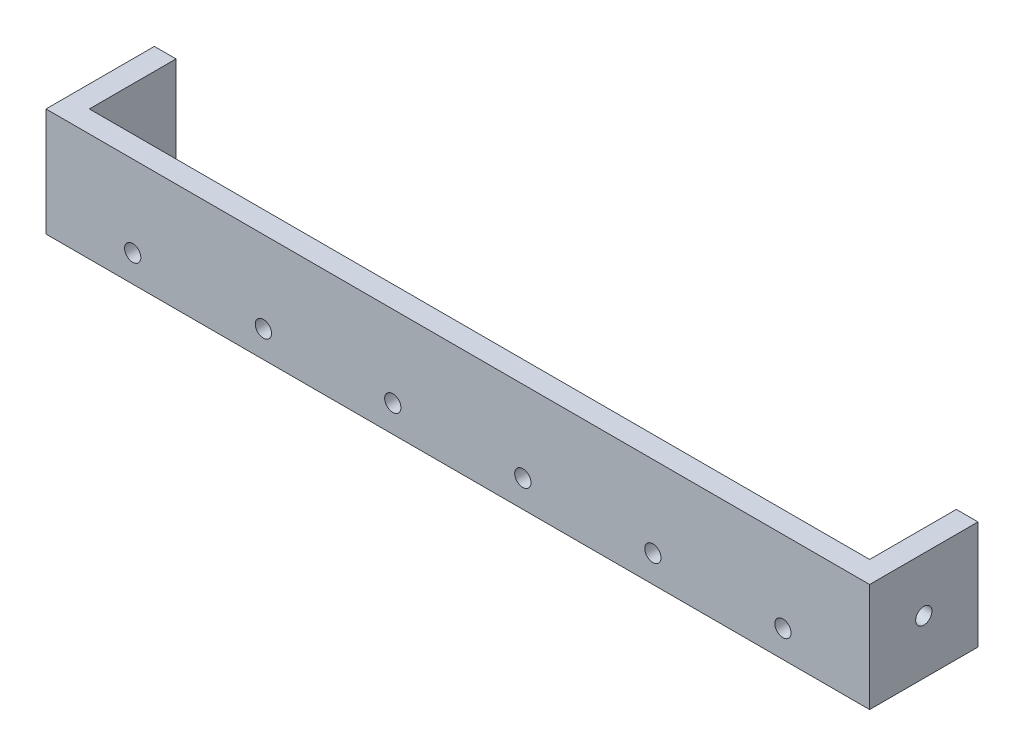
SolidWorks part; units mm, degrees
ref_plane "Front Plane" through (0, 0, 0) normal (0, 0, 1) x (1, 0, 0)
ref_plane "Top Plane" through (0, 0, 0) normal (0, 1, 0) x (1, 0, 0)
ref_plane "Right Plane" through (0, 0, 0) normal (1, 0, 0) x (0, 0, -1)
sketch "Sketch1" plane through (0, 0, 0) normal (0, 0, 1) x (1, 0, 0)
  line L0 (0, 0) -> (36, 0) construction
  line L1 (0, 0) -> (72, 0)
  line L2 (0, 0) -> (0, 10)
  line L3 (0, 10) -> (72, 10)
  line L4 (72, 0) -> (72, 10)
  line L5 (36, 0) -> (36, 18.4023) construction
sketch "Sketch3" plane through (0, 0, 0) normal (0, 0, 1) x (1, 0, 0)
  line L0 (36, 0) -> (36, 2.5) construction
  line L1 (36, 0) -> (36, 18.4023) construction
  line L2 (36, 2.5) -> (30, 2.5) construction
  line L3 (30, 2.5) -> (18, 2.5) construction
  line L4 (18, 2.5) -> (6, 2.5) construction
  line L5 (36, 2.5) -> (42, 2.5) construction
  line L6 (42, 2.5) -> (54, 2.5) construction
  line L7 (54, 2.5) -> (66, 2.5) construction
  circle A0 centre (42, 2.5) radius 0.75
  circle A1 centre (54, 2.5) radius 0.75
  circle A2 centre (66, 2.5) radius 0.75
  circle A6 centre (30, 2.5) radius 0.75
  circle A7 centre (18.0602, 2.4636) radius 0.75
  circle A8 centre (6, 2.5) radius 0.75
extrude "Boss-Extrude1" add sketch "Sketch1" along normal blind 2
extrude "Cut-Extrude2" cut sketch "Sketch3" along normal blind 2
ref_plane "Plane1" through (72, 0, 0) normal (1, 0, 0) x (0, 0, -1)
sketch "Sketch4" plane through (72, 0, 0) normal (1, 0, 0) x (0, 0, -1)
  line L1 (-2, 10) -> (8, 10)
  line L2 (-2, 10) -> (-2, 0)
  line L3 (-2, 0) -> (8, 0)
  line L4 (8, 10) -> (8, 0)
extrude "Boss-Extrude2" add sketch "Sketch4" along normal blind 2
sketch "Sketch5" plane through (72, 0, 0) normal (1, 0, 0) x (0, 0, -1)
  line L0 (-2, 10) -> (-2, 5) construction
  line L1 (-2, 10) -> (-2, 0) construction
  line L2 (-2, 5) -> (3, 5) construction
  circle A0 centre (3, 5) radius 0.75
extrude "Cut-Extrude4" cut sketch "Sketch5" along normal blind 2
ref_plane "Plane2" through (0, 0, 0) normal (-1, 0, 0) x (0, 0, 1)
sketch "Sketch6" plane through (0, 0, 0) normal (-1, 0, 0) x (0, 0, 1)
  line L1 (2, 0) -> (-8, 0)
  line L2 (2, 0) -> (2, 10)
  line L3 (2, 10) -> (-8, 10)
  line L4 (-8, 0) -> (-8, 10)
extrude "Boss-Extrude3" add sketch "Sketch6" along normal blind 2
sketch "Sketch7" plane through (0, 0, 0) normal (-1, 0, 0) x (0, 0, 1)
  line L3 (-3, 0) -> (-3, 2.5) construction
  line L4 (-8, 0) -> (2, 0) construction
  circle A0 centre (-3, 2.5) radius 0.75
  point P0 (-3, 2.4002)
  point P11 (-3, 5)
  point P12 (-3, 5)
extrude "Cut-Extrude5" cut sketch "Sketch7" along normal blind 2
